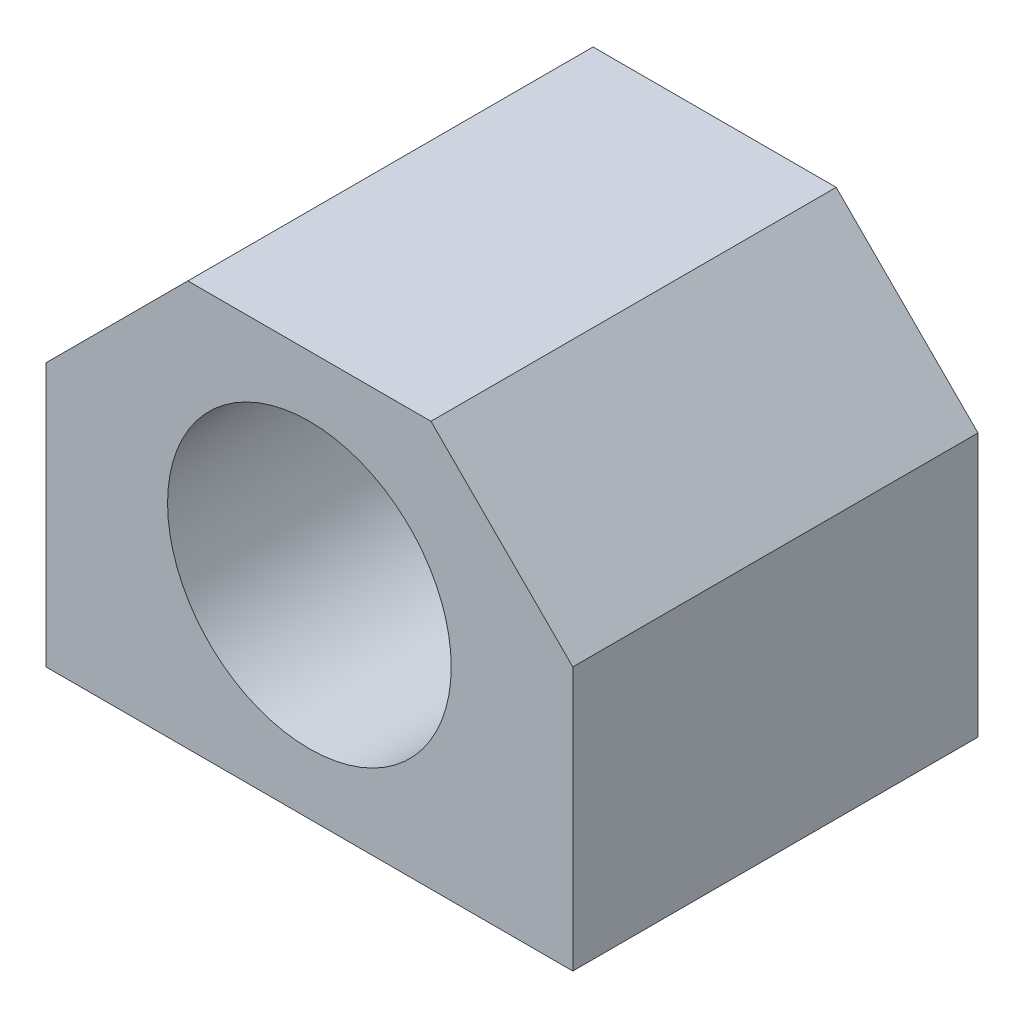
SolidWorks part; units mm, degrees
ref_plane "Ebene vorne" through (0, 0, 0) normal (0, 0, 1) x (1, 0, 0)
ref_plane "Ebene oben" through (0, 0, 0) normal (0, 1, 0) x (1, 0, 0)
ref_plane "Ebene rechts" through (0, 0, 0) normal (1, 0, 0) x (0, 0, -1)
sketch "Skizze1" plane through (0, 0, 0) normal (0, 0, 1) x (1, 0, 0)
  line L0 (-26, 0) -> (26, 0)
  line L1 (26, 0) -> (26, 26)
  line L2 (26, 26) -> (12, 40)
  line L3 (12, 40) -> (-12, 40)
  line L4 (-12, 40) -> (-26, 26)
  line L5 (-26, 26) -> (-26, 0)
  dimension "D1" = 52
  dimension "D2" = 40
  dimension "D3" = 135
  dimension "D4" = 135
  dimension "D5" = 14
  dimension "D6" = 14
  dimension "D7" = 26
extrude "Aufsatz-Linear austragen1" add sketch "Skizze1" along normal blind 40
sketch "Skizze2" plane through (0, 0, 40) normal (0, 0, 1) x (1, 0, 0)
  line L0 (-26, 26) -> (-26, 0) construction
  circle A0 centre (0, 20) radius 14
  dimension "D1" = 28
  dimension "D2" = 20
  dimension "D3" = 26
extrude "Schnitt-Linear austragen1" cut sketch "Skizze2" against normal blind 40
sketch "Skizze3" plane through (0, 0, 0) normal (0, -1, 0) x (1, 0, 0)
  line L0 (-26, 0) -> (26, 0) construction
  circle A0 centre (-20, 32) radius 2.1
  circle A1 centre (20, 32) radius 2.1
  circle A2 centre (-20, 8) radius 2.1
  circle A3 centre (20, 8) radius 2.1
  point P8 (0, 0)
  point P9 (0, 0)
  point P10 (0, 0)
  point P11 (0, 0)
  point P12 (0, 0)
  point P15 (0, 0)
  point P17 (0, 0)
  point P19 (0, 0)
  point P20 (0, 0)
  dimension "D1" = 4.2
  dimension "D2" = 4.2
  dimension "D3" = 4.2
  dimension "D4" = 4.2
  dimension "D5" = 8
  dimension "D6" = 40
  dimension "D7" = 20
  dimension "D8" = 24
extrude "Schnitt-Linear austragen2" cut sketch "Skizze3" against normal blind 15
